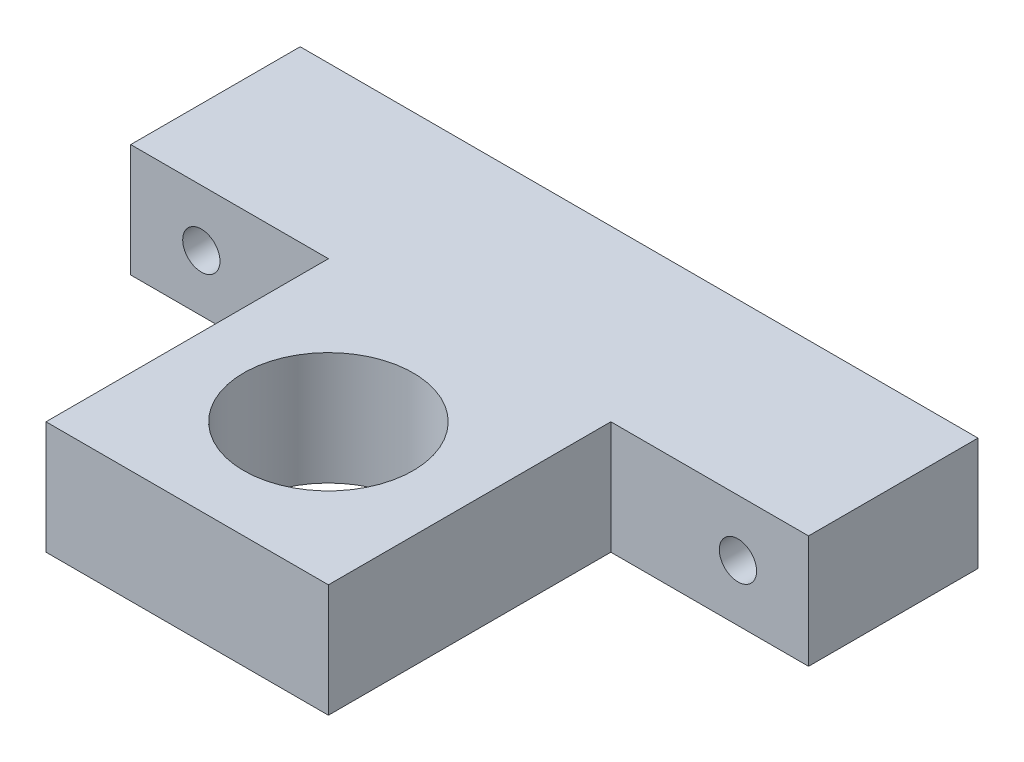
SolidWorks part; units mm, degrees
ref_plane "前基準面" through (0, 0, 0) normal (0, 0, 1) x (1, 0, 0)
ref_plane "上基準面" through (0, 0, 0) normal (0, 1, 0) x (1, 0, 0)
ref_plane "右基準面" through (0, 0, 0) normal (1, 0, 0) x (0, 0, -1)
sketch "草圖2" plane through (0, 0, 0) normal (0, 1, 0) x (1, 0, 0)
  line L0 (-12.5, -40) -> (-12.5, -15)
  line L1 (-12.5, -15) -> (-30, -15)
  line L2 (-30, -15) -> (-30, 0)
  line L3 (-30, 0) -> (30, 0)
  line L4 (0, 0) -> (0, -40) construction
  line L5 (12.5, -40) -> (-12.5, -40)
  line L6 (30, -15) -> (30, 0)
  line L7 (12.5, -15) -> (30, -15)
  line L8 (12.5, -40) -> (12.5, -15)
  line L9 (-12.5, -27.5) -> (0, -27.5) construction
  circle A0 centre (0, -27.5) radius 7.5
  dimension "D5" = 15
  dimension "D1" = 60
  dimension "D2" = 25
  dimension "D3" = 25
  dimension "D4" = 15
extrude "填料-伸長1" add sketch "草圖2" along normal mid plane 10
hole_wizard "M4 螺紋孔1" positions "草圖7" profile "草圖6" tap size "M4" standard "ISO" end condition through all
sketch "草圖7" plane through (0, 0, 0) normal (0, 0, -1) x (-1, 0, 0)
  line L0 (-23.75, 0) -> (23.75, 0) construction
  point P0 (-23.75, 0)
  point P2 (23.75, 0)
  dimension "D1" = 47.5
sketch "草圖6" plane through (23.75, 0, 0) normal (1, 0, 0) x (0, 1, 0)
  line L0 (0, 0) -> (0, 40)
  line L1 (0, 40) -> (1.65, 40)
  line L2 (1.65, 40) -> (1.65, 0)
  line L5 (1.65, 0) -> (0, 0)
  line L11 (0, -6.35) -> (0, 107.95) construction
  dimension "貫穿螺孔鑽直徑" = 3.3
  dimension "貫穿螺孔鑽深度" = 40
cosmetic thread "鑽孔螺紋1" parameters "D2"=4
cosmetic thread "鑽孔螺紋2" parameters "D2"=4
cosmetic thread "裝飾螺紋線1" parameters "D2"=4
cosmetic thread "裝飾螺紋線2" parameters "D2"=4
sketch "草圖8" plane through (0, 0, 0) normal (0, 0, -1) x (-1, 0, 0)
  point P0 (-23.75, 0)
  point P1 (23.75, 0)
